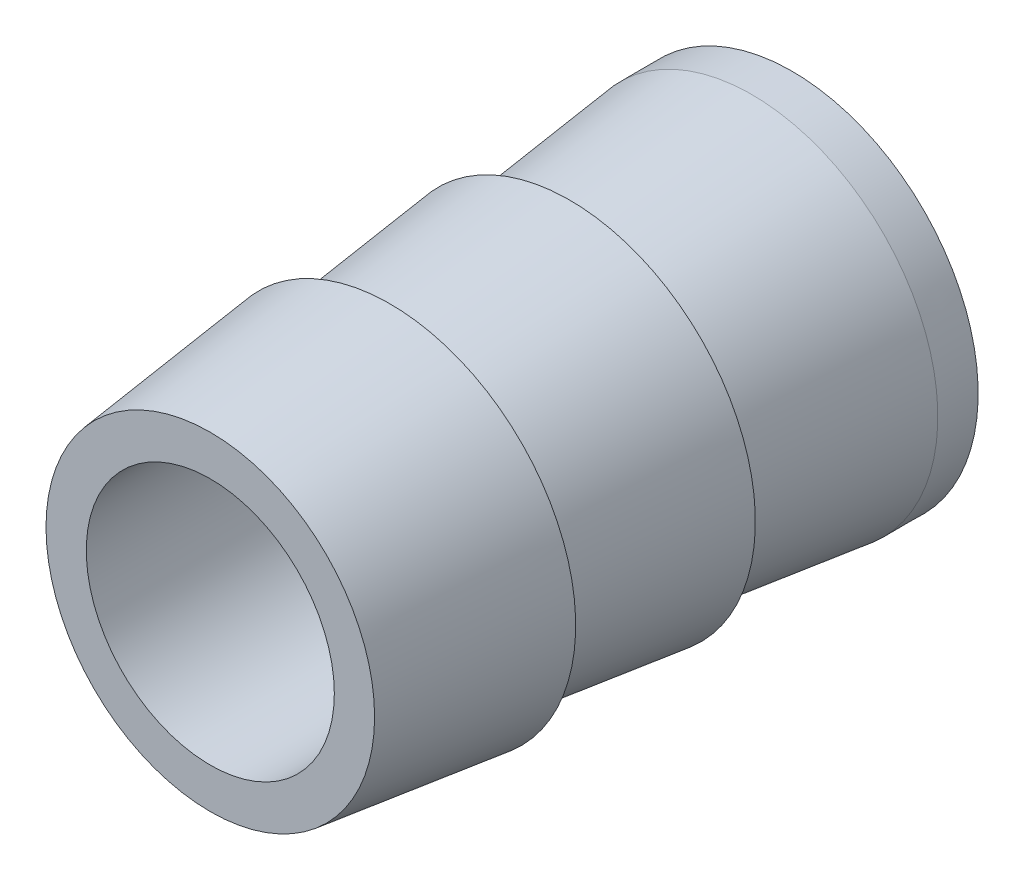
SolidWorks part; units mm, degrees
ref_plane "Front Plane" through (0, 0, 0) normal (0, 0, 1) x (1, 0, 0)
ref_plane "Top Plane" through (0, 0, 0) normal (0, 1, 0) x (1, 0, 0)
ref_plane "Right Plane" through (0, 0, 0) normal (1, 0, 0) x (0, 0, -1)
sketch "Sketch2" plane through (0, 0, 0) normal (1, 0, 0) x (0, 0, -1)
  line L0 (8.7392, 0) -> (-6.1547, 0)
  line L1 (8.7392, 0) -> (15.2797, 0) construction
  line L2 (-6.1547, 0) -> (-6.1547, 4.2059)
  line L15 (-6.0056, 4.2237) -> (-1.5549, 4.7536)
  line L16 (-1.5549, 4.7536) -> (-1.5549, 4.2059)
  line L20 (-1.4058, 4.2237) -> (3.0449, 4.7536)
  line L23 (3.0449, 4.7536) -> (3.0449, 4.2059)
  line L24 (3.194, 4.2237) -> (7.708, 4.7612)
  line L27 (7.708, 4.7612) -> (8.7392, 4.7625)
  line L30 (-6.0056, 4.2237) -> (-6.1547, 4.2059)
  line L31 (-1.4058, 4.2237) -> (-1.5549, 4.2059)
  line L32 (3.194, 4.2237) -> (3.0449, 4.2059)
  line L33 (8.7392, 4.7625) -> (8.7392, 0)
revolve "Barbfitting(Mcmaster)" add sketch "Sketch2" angle 360 about L0
sketch "Sketch3" plane through (0, 0, 6.1547) normal (0, 0, 1) x (1, 0, 0)
  circle A0 centre (0, 0) radius 3.175
  dimension "D1" = 6.35
extrude "Cut-Extrude1" cut sketch "Sketch3" against normal through all
